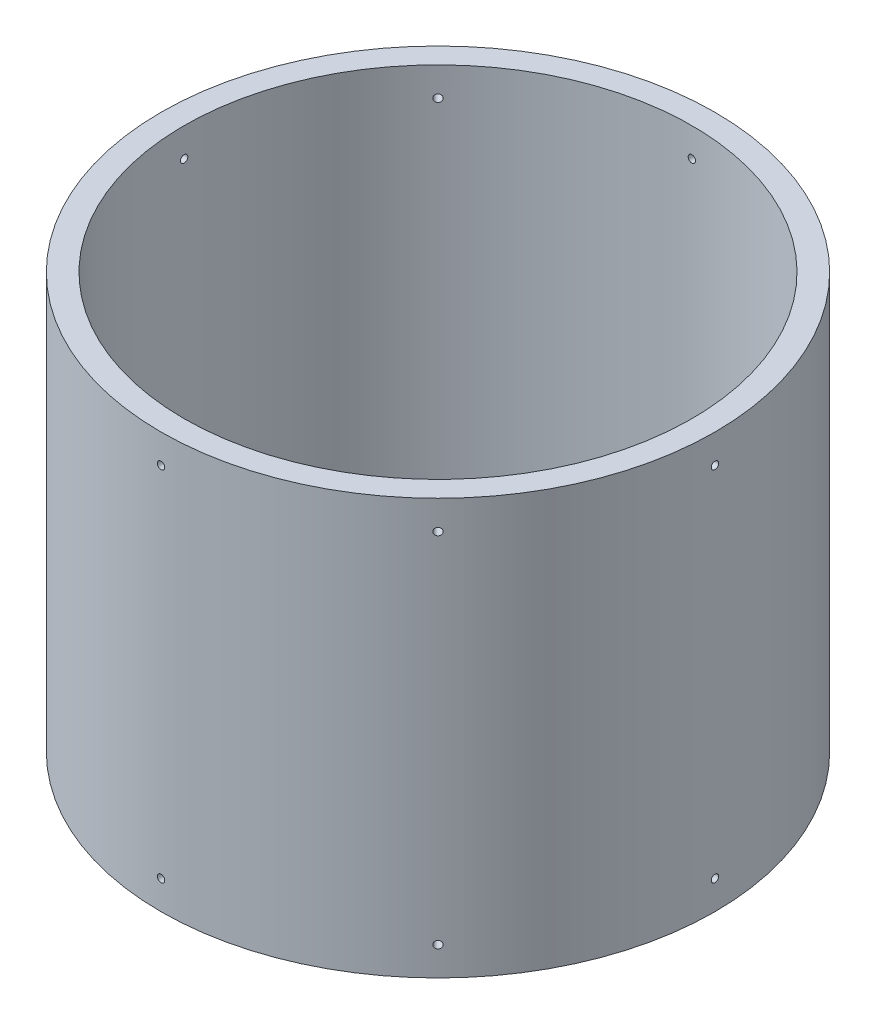
SolidWorks part; units mm, degrees
ref_plane "Front Plane" through (0, 0, 0) normal (0, 0, 1) x (1, 0, 0)
ref_plane "Top Plane" through (0, 0, 0) normal (0, 1, 0) x (1, 0, 0)
ref_plane "Right Plane" through (0, 0, 0) normal (1, 0, 0) x (0, 0, -1)
sketch "Sketch1" plane through (0, 0, 0) normal (0, 1, 0) x (1, 0, 0)
  circle A0 centre (0, 0) radius 152.4
  circle A1 centre (0, 0) radius 139.7
  dimension "D1" = 304.8
  dimension "D2" = 279.4
extrude "Boss-Extrude1" add sketch "Sketch1" along normal blind 228.6
ref_plane "Plane1" through (0, 0, 152.4) normal (0, 0, 1) x (1, 0, 0)
hole_wizard "#10-32 Tapped Hole1" positions "Sketch2" profile "Sketch3" tap size "#10-32" standard "ANSI Inch"
sketch "Sketch2" plane through (0, 0, 152.4) normal (0, 0, 1) x (1, 0, 0)
  line L0 (152.4, 228.6) -> (-152.4, 228.6) construction
  line L1 (-152.4, 0) -> (152.4, 0) construction
  line L3 (0, 212.725) -> (0, 15.875)
  line L4 (0, 15.875) -> (0, 0)
  point P0 (0, 212.725)
  point P2 (0, 15.875)
  dimension "D1" = 15.875
  dimension "D2" = 15.875
sketch "Sketch3" plane through (0, 212.725, 152.4) normal (1, 0, 0) x (0, -1, 0)
  line L0 (0, 0) -> (0, 349.967)
  line L1 (0, 349.967) -> (2.0193, 349.967)
  line L2 (2.0193, 349.967) -> (2.0193, 0)
  line L5 (2.0193, 0) -> (0, 0)
  line L11 (0, -6.35) -> (0, 107.95) construction
  dimension "Thread Major Dia." = 4.0386
  dimension "Thru Tap Drill Depth" = 349.967
pattern_circular "CirPattern1" count 8 over 360 about axis through (0, 228.6, 0) along (0, 1, 0) of "#10-32 Tapped Hole1"
